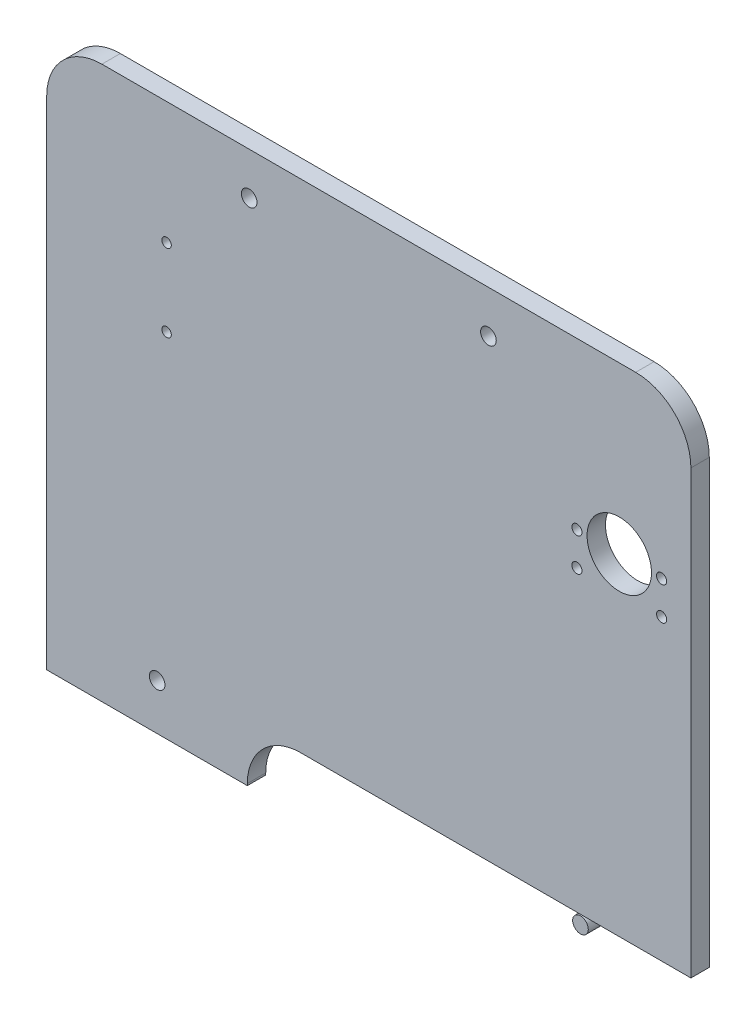
SolidWorks part; units mm, degrees
ref_plane "Alzado" through (0, 0, 0) normal (0, 0, 1) x (1, 0, 0)
ref_plane "Planta" through (0, 0, 0) normal (0, 1, 0) x (1, 0, 0)
ref_plane "Vista lateral" through (0, 0, 0) normal (1, 0, 0) x (0, 0, -1)
sketch "Croquis1" plane through (0, 0, 0) normal (0, 0, 1) x (1, 0, 0)
  line L0 (-350, 0) -> (0, 0)
  line L1 (-350, 0) -> (-350, 300)
  line L2 (-350, 300) -> (0, 300)
  line L3 (0, 0) -> (0, 300)
  dimension "D1" = 350
  dimension "D2" = 300
extrude "Saliente-Extruir1" add sketch "Croquis1" along normal blind 10
fillet "Redondeo4" radius 30 2 edges at (0, 300, 5) (-350, 300, 5)
sketch "Croquis2" plane through (0, 0, 10) normal (0, 0, 1) x (1, 0, 0)
  line L0 (-241, 0) -> (180.991, 0)
  line L1 (-241, 0) -> (-241, 1)
  line L2 (-212, 30) -> (151.991, 30)
  line L3 (180.991, 0) -> (180.991, 1)
  line L5 (-30, 300) -> (-320, 300) construction
  line L8 (-350, 270) -> (-350, 0) construction
  line L9 (0, 0) -> (0, 270) construction
  line L10 (-350, 0) -> (0, 0) construction
  arc A0 (151.991, 30) -> (180.991, 1) centre (151.991, 1) cw
  arc A1 (-241, 1) -> (-212, 30) centre (-212, 1) cw
  circle A2 centre (-38.9132, 210) radius 17.5
  circle A3 centre (-290, 25) radius 4.25
  circle A4 centre (-240, 277) radius 4.25
  circle A5 centre (-110, 277) radius 4.25
  circle A6 centre (-60, 25) radius 4.25
  circle A7 centre (-355.107, 233.567) radius 2.555
  circle A8 centre (-284.869, 233.567) radius 2.555
  circle A9 centre (-284.869, 191.548) radius 2.555
  circle A10 centre (-355.107, 191.548) radius 2.555
  circle A11 centre (-15.9132, 210) radius 2.75
  circle A12 centre (-15.9132, 192) radius 2.75
  circle A13 centre (-61.9132, 210) radius 2.75
  circle A14 centre (-61.9132, 192) radius 2.75
  point P20 (-350, 135)
  dimension "D4" = 29
  dimension "D5" = 35
  dimension "D13" = 8.5
  dimension "D14" = 60
  dimension "D19" = 5.11
  dimension "D25" = 5.5
  dimension "D1" = 421.991
  dimension "D2" = 30
  dimension "D3" = 109
  dimension "D6" = 90
  dimension "D7" = 320
  dimension "D8" = 23
  dimension "D9" = 110
  dimension "D10" = 110
  dimension "D11" = 25
  dimension "D12" = 60
  dimension "D15" = 66.433
  dimension "D16" = 284.869
  dimension "D17" = 70.238
  dimension "D18" = 42.019
  dimension "D20" = 18
  dimension "D21" = 18
  dimension "D22" = 90
  dimension "D23" = 23
  dimension "D24" = 46
extrude "Cortar-Extruir1" cut sketch "Croquis2" against normal through all
